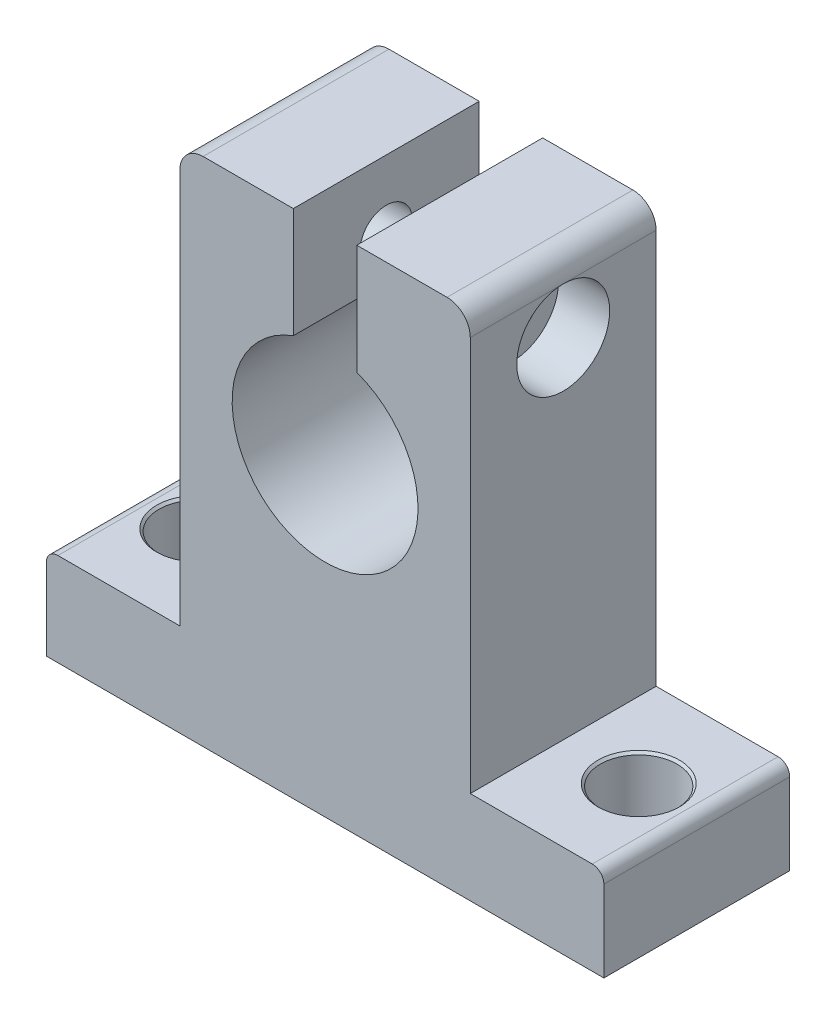
SolidWorks part; units mm, degrees
ref_plane "Front Plane" through (0, 0, 0) normal (0, 0, 1) x (1, 0, 0)
ref_plane "Top Plane" through (0, 0, 0) normal (0, 1, 0) x (1, 0, 0)
ref_plane "Right Plane" through (0, 0, 0) normal (1, 0, 0) x (0, 0, -1)
sketch "Sketch1" plane through (0, 0, 0) normal (0, 0, 1) x (1, 0, 0)
  line L0 (0, 0) -> (0, 54.5199) construction
  line L1 (24, 0) -> (-24, 0)
  line L2 (-24, 0) -> (-24, 7)
  line L3 (-23, 8) -> (-12.5, 8)
  line L4 (-12.5, 8) -> (-12.5, 42)
  line L5 (-10.5, 44) -> (-2.7317, 44)
  line L6 (-2.7317, 44) -> (-2.7317, 34.5192)
  line L7 (10.5, 44) -> (2.7317, 44)
  line L8 (2.7317, 44) -> (2.7317, 34.5192)
  line L9 (23, 8) -> (12.5, 8)
  line L10 (24, 0) -> (24, 7)
  line L11 (12.5, 8) -> (12.5, 42)
  arc A0 (-2.7317, 34.5192) -> (2.7317, 34.5192) centre (0, 27) ccw
  arc A1 (-24, 7) -> (-23, 8) centre (-23, 7) cw
  arc A2 (-12.5, 42) -> (-10.5, 44) centre (-10.5, 42) cw
  arc A3 (12.5, 42) -> (10.5, 44) centre (10.5, 42) ccw
  arc A4 (24, 7) -> (23, 8) centre (23, 7) ccw
  dimension "D1" = 16
  dimension "D7" = 1
  dimension "D8" = 2
  dimension "D2" = 27
  dimension "D3" = 24
  dimension "D4" = 11.5
  dimension "D6" = 44
extrude "Boss-Extrude1" add sketch "Sketch1" along normal blind 16
sketch "Sketch2" plane through (0, 8, 0) normal (0, 1, 0) x (1, 0, 0)
  line L0 (0, 0) -> (0, -16) construction
  line L1 (-8, -16) -> (8, -16) construction
  line L2 (-23, -8) -> (0, -8) construction
  line L3 (-23, -16) -> (-23, 0) construction
  circle A0 centre (-19, -8) radius 3.1441
  circle A1 centre (19, -8) radius 3.1441
  dimension "D1" = 19
hole_wizard "CSK for M5 Hex Socket Countersunk Cap Screw1" positions "3DSketch1" profile "Sketch3" countersink size "M5" standard "ISO" end condition through all
sketch3d "3DSketch1"
  point P0 (-19, 8, 8)
  point P3 (19, 8, 8)
sketch "Sketch3" plane through (-19, 8, 8) normal (1, 0, 0) x (0, 0, 1)
  line L0 (0, 0) -> (0, 8)
  line L1 (0, 8) -> (3.3, 8)
  line L2 (3.3, 8) -> (3.3, 0.2)
  line L3 (3.3, 0.2) -> (3.5, 0)
  line L5 (3.5, 0) -> (0, 0)
  line L6 (-3.3, 0.2) -> (-3.5, 0) construction
  line L11 (0, -6.35) -> (0, 107.95) construction
  dimension "Thru Hole Dia." = 6.6
  dimension "Thru Hole Depth" = 8
  dimension "Near C'Sink Dia." = 7
  dimension "Near C'Sink Angle" = 90
sketch "Sketch4" plane through (12.5, 0, 0) normal (1, 0, 0) x (0, 0, -1)
  line L0 (-8, 44) -> (-8, 0) construction
  line L1 (-16, 44) -> (0, 44) construction
  line L2 (-16, 0) -> (0, 0) construction
  circle A0 centre (-8, 38) radius 2.5
  dimension "D2" = 5
  dimension "D1" = 6
hole_wizard "CBORE for M4 Hex Socket Head Cap Screw1" positions "3DSketch2" profile "Sketch5" counterbore size "M4" standard "ISO" end condition through all
sketch3d "3DSketch2"
  point P0 (12.5, 38, 8)
sketch "Sketch5" plane through (12.5, 38, 8) normal (0, 1, 0) x (0, 0, -1)
  line L0 (0, 0) -> (0, 36.5)
  line L1 (0, 36.5) -> (2.25, 36.5)
  line L3 (2.25, 36.5) -> (2.25, 4.4)
  line L4 (2.25, 4.4) -> (4, 4.4)
  line L5 (4, 4.4) -> (4, 0)
  line L7 (4, 0) -> (0, 0)
  line L11 (0, -6.35) -> (0, 107.95) construction
  dimension "Thru Hole Dia." = 4.5
  dimension "Thru Hole Depth" = 36.5
  dimension "C'Bore Dia." = 8
  dimension "C'Bore Depth" = 4.4
